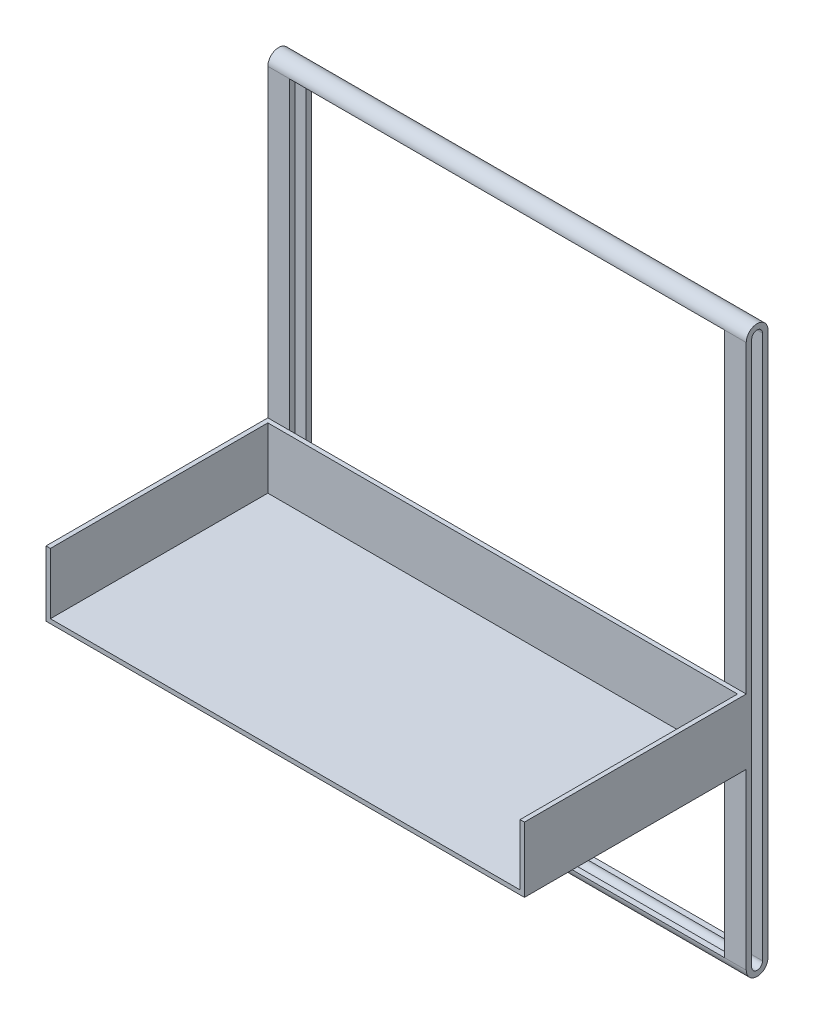
SolidWorks part; units mm, degrees
ref_plane "Plan de face" through (0, 0, 0) normal (0, 0, 1) x (1, 0, 0)
ref_plane "Plan de dessus" through (0, 0, 0) normal (0, 1, 0) x (1, 0, 0)
ref_plane "Plan de droite" through (0, 0, 0) normal (1, 0, 0) x (0, 0, -1)
sketch "Esquisse1" plane through (0, 0, 0) normal (1, 0, 0) x (0, 0, -1)
  line L2 (0, 0) -> (0, -250)
  line L4 (10, 0) -> (10, -250)
  arc A0 (10, 0) -> (0, 0) centre (5, 0) ccw
  arc A1 (10, -250) -> (0, -250) centre (5, -250) cw
  dimension "D1" = 10
  dimension "D2" = 250
extrude "Boss.-Extru.1" add sketch "Esquisse1" along normal blind 220
sketch "Esquisse2" plane through (0, 0, 0) normal (-1, 0, 0) x (0, 0, 1)
  line L0 (-7.5, 0) -> (-7.5, -250)
  line L1 (-2.5, 0) -> (-2.5, -250)
  arc A0 (-7.5, 0) -> (-2.5, 0) centre (-5, 0) cw
  arc A1 (-7.5, -250) -> (-2.5, -250) centre (-5, -250) ccw
  dimension "D1" = 2.5
  dimension "D2" = 250
  dimension "D3" = 250
extrude "Enlèv. mat.-Extru.1" cut sketch "Esquisse2" against normal up to next
sketch "Esquisse4" plane through (0, 0, 0) normal (0, 0, 1) x (1, 0, 0)
  line L0 (220, 0) -> (0, 0) construction
  line L1 (10, 0) -> (210, 0)
  line L2 (10, 0) -> (10, -250)
  line L3 (10, -250) -> (210, -250)
  line L4 (210, 0) -> (210, -250)
  line L5 (220, -250) -> (0, -250) construction
  line L6 (0, 0) -> (0, -250) construction
  line L7 (220, 0) -> (220, -250) construction
  dimension "D1" = 0
  dimension "D2" = 0
  dimension "D3" = 10
  dimension "D4" = 10
extrude "Enlèv. mat.-Extru.2" cut sketch "Esquisse4" against normal blind 200
sketch "Esquisse5" plane through (0, 0, 0) normal (0, 0, 1) x (1, 0, 0)
  line L0 (0, 0) -> (0, -250) construction
  line L1 (0, -140) -> (220, -140)
  line L2 (0, -140) -> (0, -170)
  line L3 (0, -170) -> (220, -170)
  line L4 (220, -140) -> (220, -170)
  line L5 (220, 0) -> (220, -250) construction
  line L6 (210, 0) -> (10, 0) construction
  dimension "D1" = 140
  dimension "D2" = 30
extrude "Boss.-Extru.2" add sketch "Esquisse5" along normal blind 2
sketch "Esquisse7" plane through (0, 0, 2) normal (0, 0, 1) x (1, 0, 0)
  line L0 (220, -170) -> (220, -140) construction
  line L1 (0, -170) -> (220, -170)
  line L2 (0, -170) -> (0, -168)
  line L3 (0, -168) -> (220, -168)
  line L4 (220, -170) -> (220, -168)
  dimension "D1" = 2
extrude "Boss.-Extru.4" add sketch "Esquisse7" along normal blind 100
sketch "Esquisse8" plane through (0, 0, 2) normal (0, 0, 1) x (1, 0, 0)
  line L0 (220, -140) -> (0, -140) construction
  line L1 (0, -168) -> (2, -168)
  line L2 (0, -168) -> (0, -140)
  line L3 (0, -140) -> (2, -140)
  line L4 (2, -168) -> (2, -140)
  line L5 (220, -140) -> (210, -140) construction
  line L6 (220, -168) -> (218, -168)
  line L7 (220, -168) -> (220, -140)
  line L8 (220, -140) -> (218, -140)
  line L9 (218, -168) -> (218, -140)
  dimension "D1" = 2
  dimension "D2" = 2
extrude "Boss.-Extru.5" add sketch "Esquisse8" along normal blind 100
